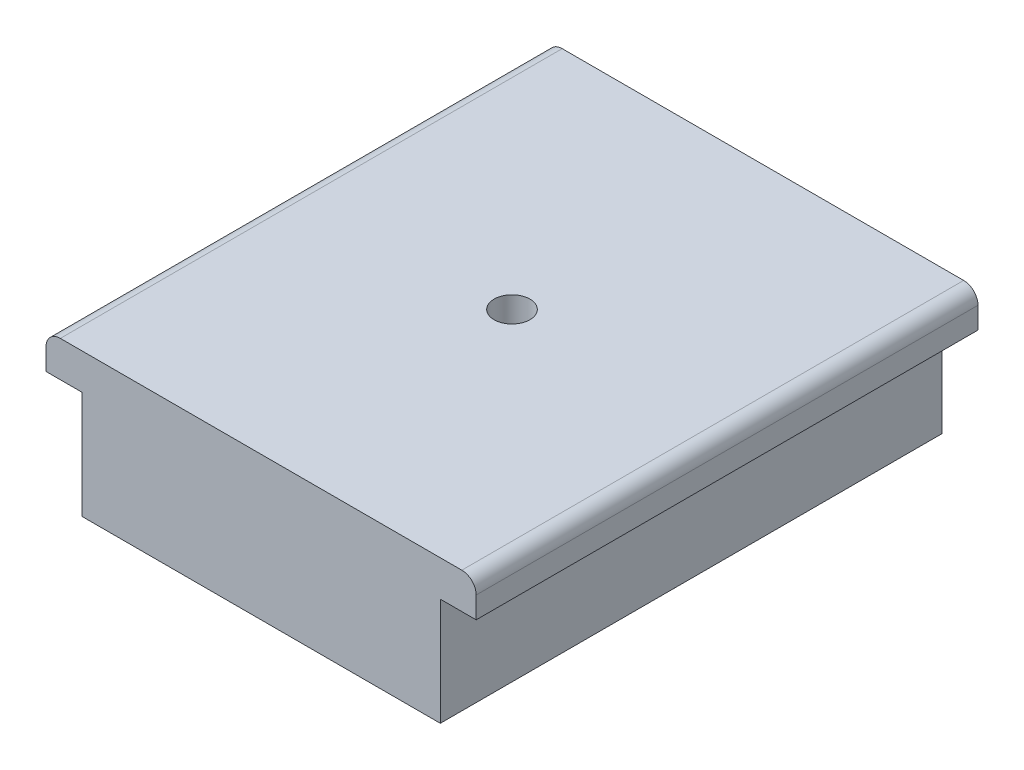
SolidWorks part; units mm, degrees
ref_plane "Front Plane" through (0, 0, 0) normal (0, 0, 1) x (1, 0, 0)
ref_plane "Top Plane" through (0, 0, 0) normal (0, 1, 0) x (1, 0, 0)
ref_plane "Right Plane" through (0, 0, 0) normal (1, 0, 0) x (0, 0, -1)
sketch "Sketch1" plane through (0, 0, 0) normal (0, 0, 1) x (1, 0, 0)
  line L1 (25, -7.5) -> (-25, -7.5)
  line L2 (25, -7.5) -> (25, 7.5)
  line L3 (25, 7.5) -> (-25, 7.5)
  line L4 (-25, -7.5) -> (-25, 7.5)
  line L5 (0, 7.5) -> (0, -7.5) construction
  line L6 (25, 0) -> (-25, 0) construction
  point P0 (0, 0)
  dimension "D1" = 15
  dimension "D2" = 50
extrude "Boss-Extrude1" add sketch "Sketch1" along normal mid plane 70
sketch "Sketch3" plane through (0, 7.5, 0) normal (0, 1, 0) x (1, 0, 0)
  line L0 (25, 35) -> (-25, 35) construction
  line L1 (30, 35) -> (-30, 35)
  line L2 (30, 35) -> (30, -35)
  line L3 (30, -35) -> (-30, -35)
  line L4 (-30, 35) -> (-30, -35)
  line L5 (0, -35) -> (0, 35) construction
  line L6 (30, 0) -> (-30, 0) construction
  point P0 (0, 0)
  dimension "D1" = 60
extrude "Boss-Extrude2" add sketch "Sketch3" along normal blind 5
ref_plane "Plane1" through (0, 12.5, 0) normal (0, 1, 0) x (1, 0, 0)
sketch "Sketch2" plane through (0, 12.5, 0) normal (0, 1, 0) x (1, 0, 0)
  circle A0 centre (0, 0) radius 2.5
  point P2 (0, 0)
  dimension "D1" = 5
extrude "Cut-Extrude1" cut sketch "Sketch2" against normal blind 10 and the other way through all
fillet "Fillet1" radius 2 2 edges at (-30, 12.5, 0) (30, 12.5, 0)
